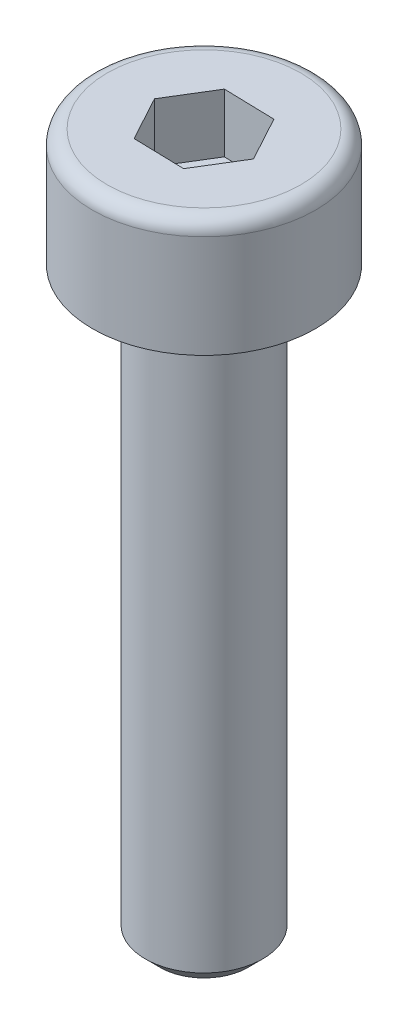
SolidWorks part; units mm, degrees
material "Alu Alliage 2017 Dural"
ref_plane "Plan de face" through (0, 0, 0) normal (0, 0, 1) x (1, 0, 0)
ref_plane "Plan de dessus" through (0, 0, 0) normal (0, 1, 0) x (1, 0, 0)
ref_plane "Plan de droite" through (0, 0, 0) normal (1, 0, 0) x (0, 0, -1)
sketch "DIAMETRE_TETE" plane through (0, 0, 0) normal (0, 1, 0) x (1, 0, 0)
  circle A0 centre (0, 0) radius 1.9
  dimension "D1" = 3.8
extrude "HAUTEUR_TETE" add sketch "DIAMETRE_TETE" along normal blind 2
fillet "CONGE" radius 0.25 1 edges at (0, 2, 1.9)
sketch "DIAMETRE" plane through (0, 0, 0) normal (0, -1, 0) x (1, 0, 0)
  circle A0 centre (0, 0) radius 1
  dimension "D1" = 2
extrude "LONGUEUR" add sketch "DIAMETRE" along normal blind 10
cosmetic thread "LONGUEUR_FILETAGE" parameters "HAUTEUR_FILETAGE"=10, "D2"=1.202
sketch "LARGEUR_6PANS" plane through (0, 2, 0) normal (0, 1, 0) x (1, 0, 0)
  line L1 (0.4524, 0.7385) -> (-0.4134, 0.761)
  line L2 (-0.4134, 0.761) -> (-0.8657, 0.0225)
  line L3 (-0.8657, 0.0225) -> (-0.4524, -0.7385)
  line L4 (-0.4524, -0.7385) -> (0.4134, -0.761)
  line L5 (0.4134, -0.761) -> (0.8657, -0.0225)
  line L6 (0.8657, -0.0225) -> (0.4524, 0.7385)
  circle A0 centre (0, 0) radius 0.75 construction
  dimension "D1" = 1.5
extrude "HAUTEUR_6PANS" cut sketch "LARGEUR_6PANS" against normal blind 1
chamfer "CHANFREIN" distance 0.25 angle 45 1 edges at (0, -10, -1)
